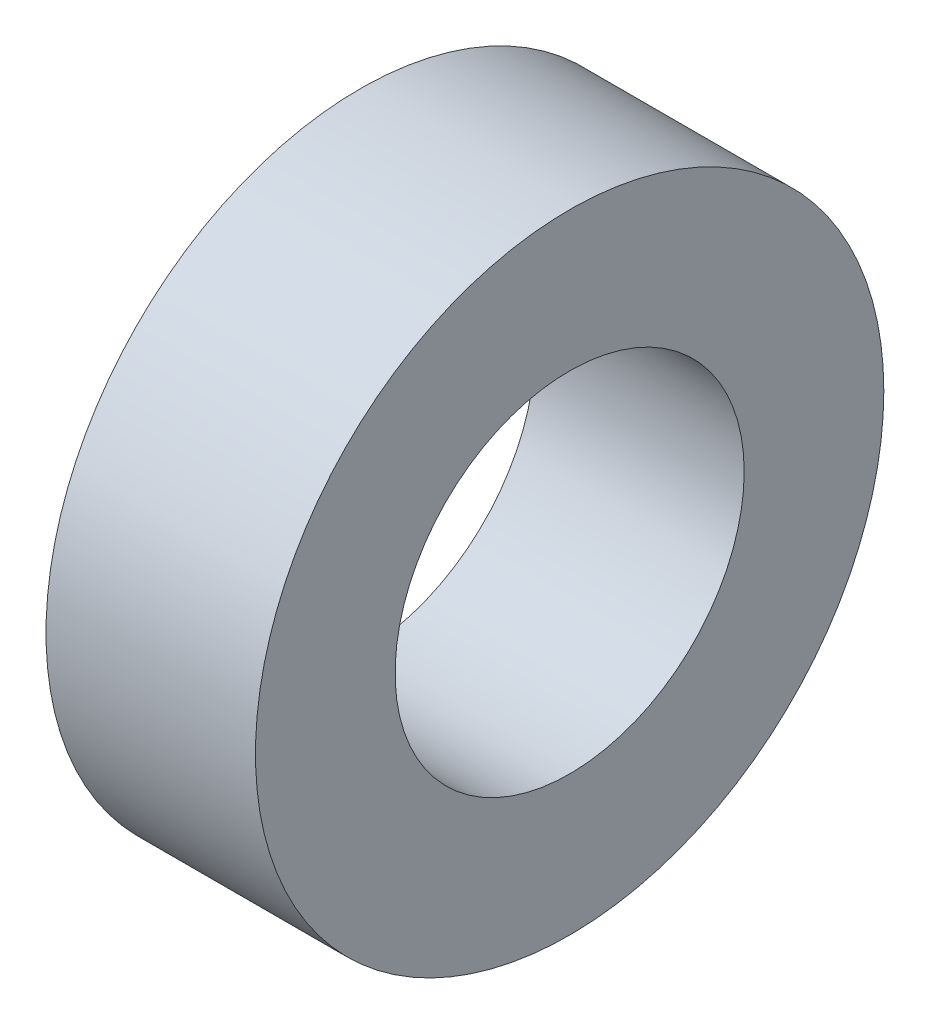
SolidWorks part; units mm, degrees
ref_plane "前视基准面" through (0, 0, 0) normal (0, 0, 1) x (1, 0, 0)
ref_plane "上视基准面" through (0, 0, 0) normal (0, 1, 0) x (1, 0, 0)
ref_plane "右视基准面" through (0, 0, 0) normal (1, 0, 0) x (0, 0, -1)
sketch "草图1" plane through (0, 0, 0) normal (1, 0, 0) x (0, 0, -1)
  circle A0 centre (0, 0) radius 4.5
  circle A1 centre (0, 0) radius 2.5
extrude "凸台-拉伸1" add sketch "草图1" along normal blind 3
